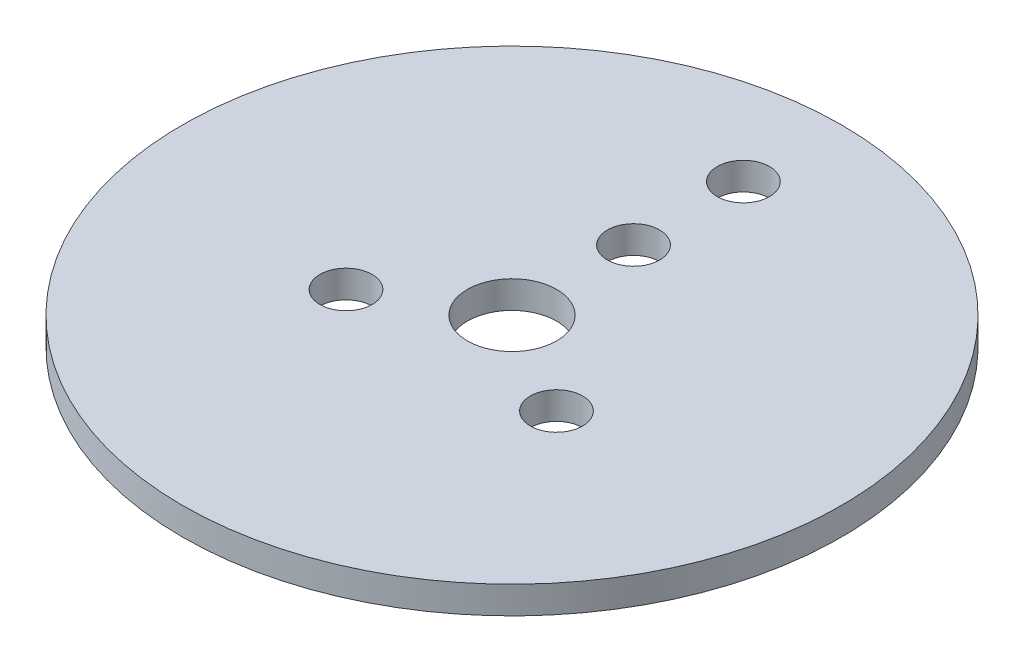
SolidWorks part; units mm, degrees
material "1060 Alloy"
ref_plane "Front Plane" through (0, 0, 0) normal (0, 0, 1) x (1, 0, 0)
ref_plane "Top Plane" through (0, 0, 0) normal (0, 1, 0) x (1, 0, 0)
ref_plane "Right Plane" through (0, 0, 0) normal (1, 0, 0) x (0, 0, -1)
sketch "Sketch1" plane through (0, 0, 0) normal (0, 1, 0) x (1, 0, 0)
  circle A0 centre (0, 0) radius 24
  dimension "D1" = 48
extrude "Boss-Extrude1" add sketch "Sketch1" along normal blind 2
sketch "Sketch2" plane through (0, 2, 0) normal (0, 1, 0) x (1, 0, 0)
  line L0 (0, -24) -> (0, 24) construction
  line L1 (23.7789, -3.25) -> (-23.7789, -3.25)
  line L2 (0, 8.85) -> (-22.3087, 8.85) construction
  line L3 (0, 10.75) -> (-21.4578, 10.75) construction
  line L4 (0, 18.75) -> (-14.9812, 18.75) construction
  line L5 (-5, 9.5164) -> (5, 9.5164) construction
  circle A0 centre (0, 0) radius 3.25
  circle A1 centre (0, 0) radius 8.85
  circle A2 centre (0, 0) radius 24 construction
  circle A3 centre (0, 8.85) radius 1.9
  circle A4 centre (7.6643, -4.425) radius 1.9
  circle A5 centre (-7.6643, -4.425) radius 1.9
  circle A6 centre (0, 0) radius 10.75
  circle A7 centre (0, 0) radius 18.75
  circle A8 centre (0, 16.85) radius 1.9
  point P12 (0, -3.25)
  point P22 (0, 0)
  point P26 (-7.4906, 18.75)
  dimension "D1" = 6.5
  dimension "D2" = 12.1
  dimension "D3" = 3.8
  dimension "D5" = 8
  dimension "D6" = 10
  dimension "D4" = 3
extrude "Cut-Extrude1" cut sketch "Sketch2" against normal through all contours A0 | L1 A5 A1 | A1 A5 L1 | L1 A5 A1 | A1 A5 L1 | L1 A4 A1 | A1 A4 L1 | A1 A4 L1 | L1 A4 A1 | A1 A3 | A1 A3 | A8
